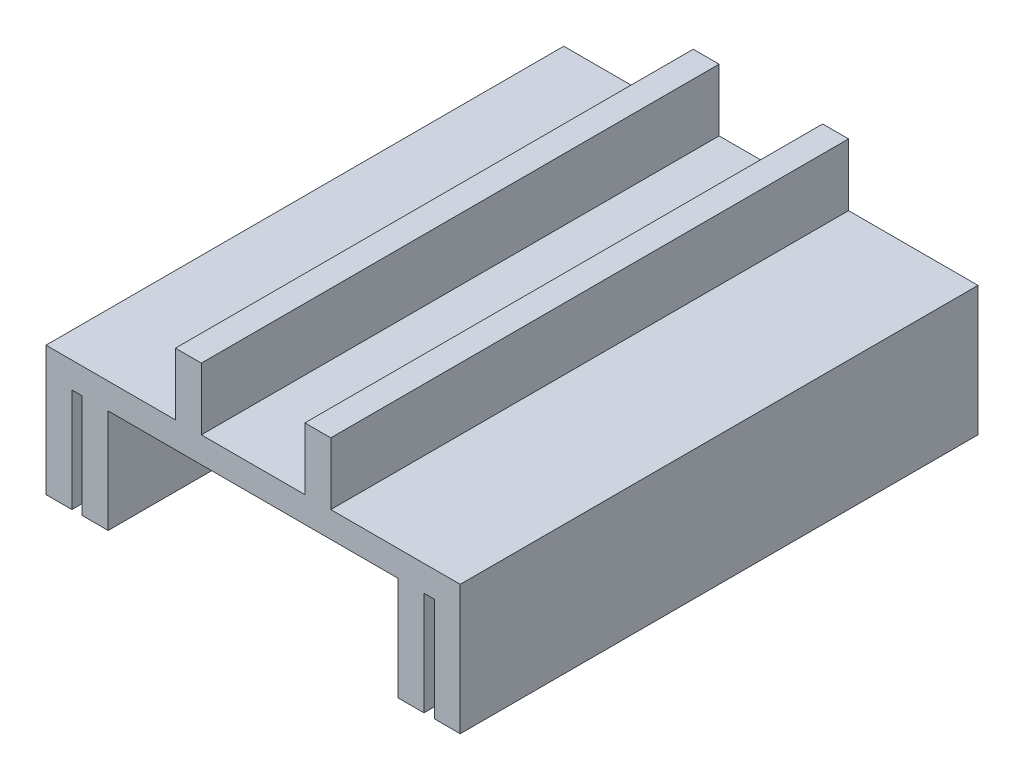
SolidWorks part; units mm, degrees
ref_plane "Plan de face" through (0, 0, 0) normal (0, 0, 1) x (1, 0, 0)
ref_plane "Plan de dessus" through (0, 0, 0) normal (0, 1, 0) x (1, 0, 0)
ref_plane "Plan de droite" through (0, 0, 0) normal (1, 0, 0) x (0, 0, -1)
sketch "Esquisse1" plane through (0, 0, 0) normal (0, 1, 0) x (1, 0, 0)
  line L1 (-40, -50) -> (40, -50)
  line L2 (-40, -50) -> (-40, 50)
  line L3 (-40, 50) -> (40, 50)
  line L4 (40, -50) -> (40, 50)
  line L5 (-40, -50) -> (40, 50) construction
  line L6 (-40, 50) -> (40, -50) construction
  point P0 (0, 0)
  dimension "D1" = 80
  dimension "D2" = 100
extrude "Boss.-Extru.1" add sketch "Esquisse1" along normal blind 5
sketch "Esquisse3" plane through (0, 0, 0) normal (0, -1, 0) x (1, 0, 0)
  line L0 (-40, 50) -> (-40, -50)
  line L1 (-40, -50) -> (-35, -50)
  line L2 (40, -50) -> (-40, -50) construction
  line L3 (-35, -50) -> (-35, 50)
  line L4 (-40, 50) -> (40, 50) construction
  line L5 (-35, 50) -> (-40, 50)
  line L6 (-33, 50) -> (-33, -50)
  line L7 (-33, -50) -> (-28, -50)
  line L8 (-28, -50) -> (-28, 50)
  line L9 (-28, 50) -> (-33, 50)
  line L10 (0, 50) -> (0, -50) construction
  line L11 (28, 50) -> (33, 50)
  line L12 (28, -50) -> (28, 50)
  line L13 (33, -50) -> (28, -50)
  line L14 (33, 50) -> (33, -50)
  line L15 (40, -50) -> (35, -50)
  line L16 (35, 50) -> (40, 50)
  line L17 (35, -50) -> (35, 50)
  line L18 (40, 50) -> (40, -50)
  dimension "D1" = 5
  dimension "D2" = 5
  dimension "D3" = 2
extrude "Boss.-Extru.2" add sketch "Esquisse3" along normal blind 20
sketch "Esquisse4" plane through (0, 5, 0) normal (0, 1, 0) x (1, 0, 0)
  line L0 (-10, 50) -> (-10, -50)
  line L1 (40, 50) -> (-40, 50) construction
  line L2 (-40, -50) -> (40, -50) construction
  line L3 (-10, -50) -> (-15, -50)
  line L4 (-15, -50) -> (-15, 50)
  line L5 (-15, 50) -> (-10, 50)
  line L6 (10, 50) -> (10, -50)
  line L7 (10, -50) -> (15, -50)
  line L8 (15, -50) -> (15, 50)
  line L9 (15, 50) -> (10, 50)
  dimension "D1" = 10
  dimension "D2" = 10
  dimension "D3" = 5
  dimension "D4" = 5
extrude "Boss.-Extru.3" add sketch "Esquisse4" along normal blind 12
